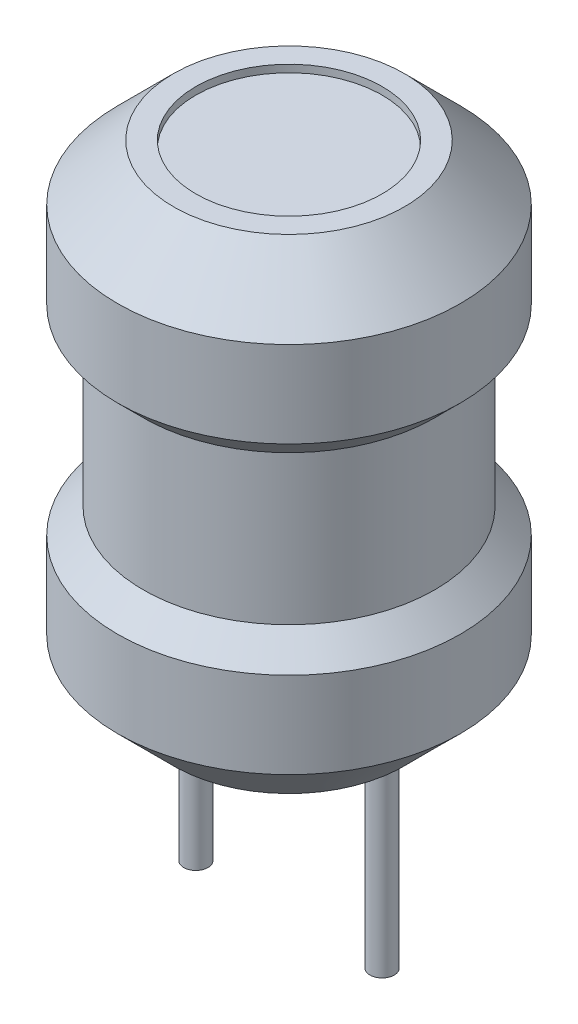
SolidWorks part; units mm, degrees
ref_plane "Спереди" through (0, 0, 0) normal (0, 0, 1) x (1, 0, 0)
ref_plane "Сверху" through (0, 0, 0) normal (0, 1, 0) x (1, 0, 0)
ref_plane "Справа" through (0, 0, 0) normal (1, 0, 0) x (0, 0, -1)
sketch "Эскиз6" plane through (0, 0, 0) normal (0, 0, 1) x (1, 0, 0)
  line L7 (0, 13) -> (0, 0)
  line L8 (0, 13) -> (3.1, 13)
  line L9 (3.1, 13) -> (4.6, 11.5)
  line L10 (4.6, 11.5) -> (4.6, 9.1876)
  line L11 (4.6, 9.1876) -> (3.9124, 8.5)
  line L12 (3.9124, 8.5) -> (3.9124, 4.5)
  line L13 (3.9124, 4.5) -> (4.6, 3.8124)
  line L14 (4.6, 3.8124) -> (4.6, 1.5)
  line L15 (4.6, 1.5) -> (3.1, 0)
  line L16 (3.1, 0) -> (0, 0)
  dimension "D1" = 13
  dimension "D2" = 4.6
  dimension "D3" = 1.5
  dimension "D4" = 1.5
  dimension "D5" = 4
revolve "Повернуть1" add sketch "Эскиз6" angle 360 about L7
sketch "Эскиз7" plane through (0, 0, 0) normal (0, -1, 0) x (1, 0, 0)
  line L0 (0, 0.7978) -> (0, -0.9886) construction
  circle A0 centre (2.5, 0) radius 0.325
  circle A1 centre (-2.5, 0) radius 0.325
  dimension "D1" = 0.65
  dimension "D2" = 2.5
extrude "Бобышка-Вытянуть1" add sketch "Эскиз7" along normal blind 5
sketch "Эскиз8" plane through (0, 13, 0) normal (0, 1, 0) x (1, 0, 0)
  circle A0 centre (0, 0) radius 2.5
extrude "Вырез-Вытянуть1" cut sketch "Эскиз8" against normal blind 0.2
